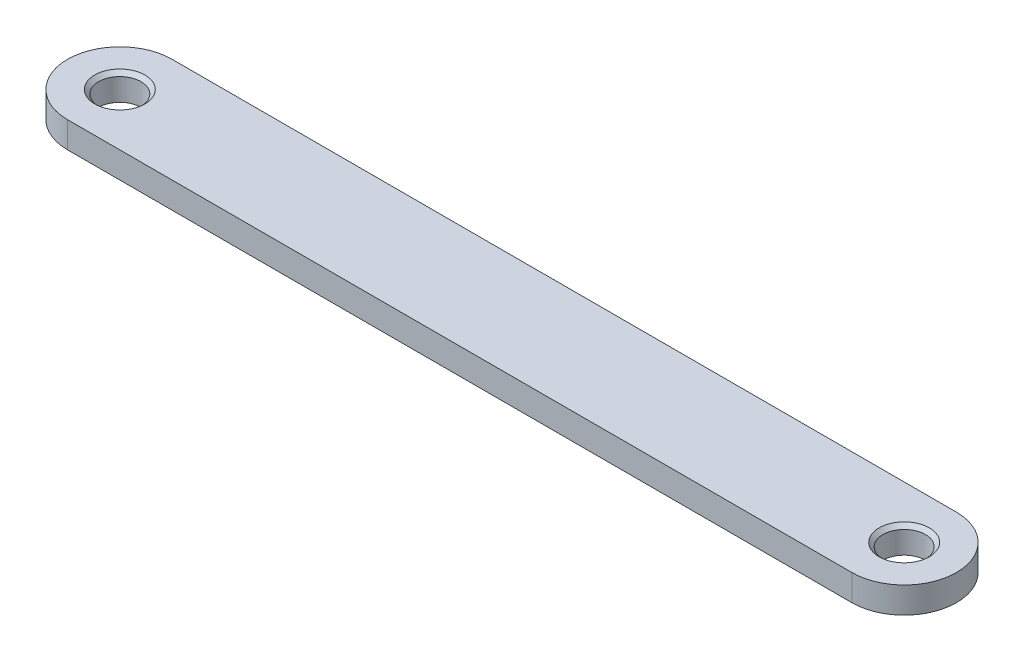
SolidWorks part; units mm, degrees
ref_plane "Front Plane" through (0, 0, 0) normal (0, 0, 1) x (1, 0, 0)
ref_plane "Top Plane" through (0, 0, 0) normal (0, 1, 0) x (1, 0, 0)
ref_plane "Right Plane" through (0, 0, 0) normal (1, 0, 0) x (0, 0, -1)
sketch "Sketch1" plane through (0, 0, 0) normal (0, 1, 0) x (1, 0, 0)
  line L0 (-47.625, 0) -> (47.625, 0) construction
  line L1 (-47.625, 6.35) -> (47.625, 6.35)
  line L2 (-47.625, -6.35) -> (47.625, -6.35)
  arc A0 (-47.625, 6.35) -> (-47.625, -6.35) centre (-47.625, 0) ccw
  arc A1 (47.625, -6.35) -> (47.625, 6.35) centre (47.625, 0) ccw
  circle A2 centre (47.625, 0) radius 2.5797
  circle A3 centre (-47.625, 0) radius 2.5797
  point P3 (0, 0)
  dimension "D2" = 6.35
  dimension "D3" = 5.1594
  dimension "D1" = 95.25
extrude "Boss-Extrude1" add sketch "Sketch1" along normal blind 3.175
hole_wizard "#10-32 Tapped Hole3" positions "Sketch6" profile "Sketch7" tap size "#10-32" standard "ANSI Inch" end condition through all
sketch "Sketch6" plane through (0, 3.175, 0) normal (0, 1, 0) x (1, 0, 0)
  point P0 (-47.625, 0)
  point P3 (47.625, 0)
sketch "Sketch7" plane through (-47.625, 3.175, 0) normal (1, 0, 0) x (0, 0, 1)
  line L0 (0, 0) -> (0, 3.175)
  line L1 (0, 3.175) -> (2.0193, 3.175)
  line L2 (2.0193, 3.175) -> (2.0193, 1.0287)
  line L3 (2.0193, 1.0287) -> (3.048, 0)
  line L5 (3.048, 0) -> (0, 0)
  line L6 (-2.0193, 1.0287) -> (-3.048, 0) construction
  line L11 (0, -6.35) -> (0, 107.95) construction
  dimension "Thru Tap Drill Dia." = 4.0386
  dimension "Thru Tap Drill Depth" = 3.175
  dimension "Near C'Sink Dia." = 6.096
  dimension "Near C'Sink Angle" = 90
